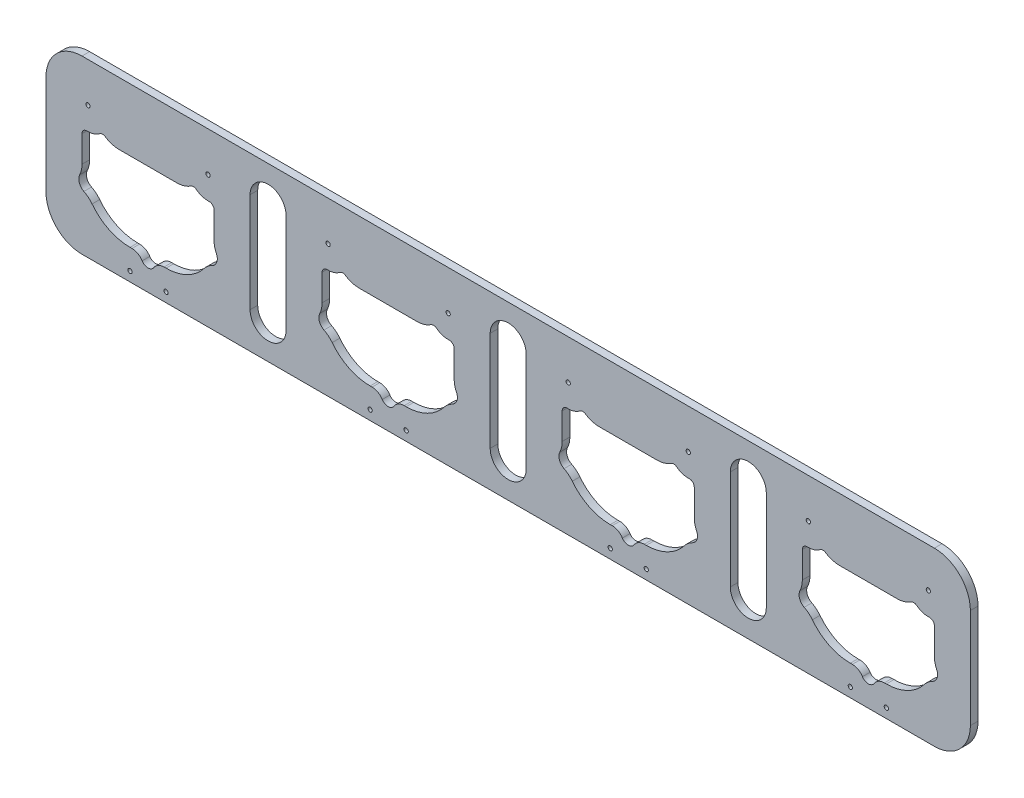
SolidWorks part; units mm, degrees
ref_plane "Front Plane" through (0, 0, 0) normal (0, 0, 1) x (1, 0, 0)
ref_plane "Top Plane" through (0, 0, 0) normal (0, 1, 0) x (1, 0, 0)
ref_plane "Right Plane" through (0, 0, 0) normal (1, 0, 0) x (0, 0, -1)
sketch "Sketch1" plane through (0, 0, 0) normal (0, 0, 1) x (1, 0, 0)
  line L1 (-5.296, 23.9144) -> (18.704, 23.9144)
  line L3 (13.382, -9.0856) -> (14.204, -9.0856)
  line L10 (34.204, 10.9144) -> (34.204, 21.927)
  line L11 (-0.796, -9.0856) -> (0.0259, -9.0856)
  line L12 (-20.796, 10.9144) -> (-20.796, 21.927)
  line L50 (94.704, 23.9144) -> (118.704, 23.9144)
  line L52 (113.382, -9.0856) -> (114.204, -9.0856)
  line L59 (134.204, 10.9144) -> (134.204, 21.927)
  line L60 (99.204, -9.0856) -> (100.0259, -9.0856)
  line L61 (79.204, 10.9144) -> (79.204, 21.927)
  line L74 (149.204, 34.9144) -> (149.204, -6.5856)
  line L75 (164.204, -6.5856) -> (164.204, 34.9144)
  line L77 (194.704, 23.9144) -> (218.704, 23.9144)
  line L79 (213.382, -9.0856) -> (214.204, -9.0856)
  line L86 (234.204, 10.9144) -> (234.204, 21.927)
  line L87 (199.204, -9.0856) -> (200.0259, -9.0856)
  line L88 (179.204, 10.9144) -> (179.204, 21.927)
  line L101 (249.204, 34.9144) -> (249.204, -6.5856)
  line L102 (264.204, -6.5856) -> (264.204, 34.9144)
  line L104 (294.704, 23.9144) -> (318.704, 23.9144)
  line L106 (313.382, -9.0856) -> (314.204, -9.0856)
  line L113 (334.204, 10.9144) -> (334.204, 21.927)
  line L114 (299.204, -9.0856) -> (300.0259, -9.0856)
  line L115 (279.204, 10.9144) -> (279.204, 21.927)
  line L153 (49.204, 34.9144) -> (49.204, -6.5856)
  line L154 (64.204, -6.5856) -> (64.204, 34.9144)
  line L159 (-20.796, 49.9144) -> (334.204, 49.9144)
  line L160 (-35.796, 34.9144) -> (-35.796, -6.5856)
  line L161 (-20.796, -21.5856) -> (334.204, -21.5856)
  line L162 (349.204, -6.5856) -> (349.204, 34.9144)
  line L163 (364.204, -6.5856) -> (364.204, 34.9144) [skipped]
  line L164 (349.204, 34.9144) -> (349.204, -6.5856) [skipped]
  arc A0 (24.4994, 25.6587) -> (18.704, 23.9144) centre (18.704, 34.4144) cw
  arc A1 (34.2039, 10.8952) -> (34.204, 10.9144) centre (14.204, 10.9144) ccw
  arc A6 (-16.6004, -1.3421) -> (-0.796, -9.0856) centre (-0.796, 10.9144) ccw
  arc A7 (34.2039, 10.8952) -> (35.1806, 6.5752) centre (44.2039, 10.8855) ccw
  arc A24 (-11.0915, 25.6587) -> (-13.4155, 25.5756) centre (-12.1954, 23.9909) ccw
  arc A25 (-20.796, 21.927) -> (-18.696, 23.9245) centre (-18.796, 21.927) cw
  arc A26 (26.8234, 25.5756) -> (32.104, 23.9245) centre (31.704, 31.9144) ccw
  arc A28 (26.8234, 25.5756) -> (24.4994, 25.6587) centre (25.6033, 23.9909) ccw
  arc A29 (14.204, -9.0856) -> (30.0083, -1.3421) centre (14.204, 10.9144) ccw
  arc A30 (-20.796, 10.9144) -> (-20.796, 10.8952) centre (-0.796, 10.9144) ccw
  arc A31 (30.0083, -1.3421) -> (33.4302, 1.4699) centre (37.9105, -7.4703) cw
  arc A33 (-18.696, 23.9245) -> (-13.4155, 25.5756) centre (-18.296, 31.9144) ccw
  arc A34 (-16.6004, -1.3421) -> (-20.0223, 1.4699) centre (-24.5026, -7.4703) ccw
  arc A36 (-20.796, 10.8952) -> (-21.7727, 6.5752) centre (-30.796, 10.8855) cw
  arc A37 (4.2584, -11.4236) -> (0.0259, -9.0856) centre (0.0259, -14.0856) ccw
  arc A38 (-11.0915, 25.6587) -> (-5.296, 23.9144) centre (-5.296, 34.4144) ccw
  arc A39 (-21.7727, 6.5752) -> (-20.0223, 1.4699) centre (-18.296, 4.9144) ccw
  arc A40 (33.4302, 1.4699) -> (35.1806, 6.5752) centre (31.704, 4.9144) ccw
  arc A41 (4.2584, -11.4236) -> (9.1495, -11.4236) centre (6.704, -9.8856) ccw
  arc A43 (34.204, 21.927) -> (32.104, 23.9245) centre (32.204, 21.927) ccw
  arc A44 (9.1495, -11.4236) -> (13.382, -9.0856) centre (13.382, -14.0856) cw
  arc A109 (124.4994, 25.6587) -> (118.704, 23.9144) centre (118.704, 34.4144) cw
  arc A110 (134.2039, 10.8952) -> (134.204, 10.9144) centre (114.204, 10.9144) ccw
  arc A115 (83.3996, -1.3421) -> (99.204, -9.0856) centre (99.204, 10.9144) ccw
  arc A116 (134.2039, 10.8952) -> (135.1806, 6.5752) centre (144.2039, 10.8855) ccw
  arc A133 (88.9085, 25.6587) -> (86.5845, 25.5756) centre (87.8046, 23.9909) ccw
  arc A134 (79.204, 21.927) -> (81.304, 23.9245) centre (81.204, 21.927) cw
  arc A135 (126.8234, 25.5756) -> (132.104, 23.9245) centre (131.704, 31.9144) ccw
  arc A137 (126.8234, 25.5756) -> (124.4994, 25.6587) centre (125.6033, 23.9909) ccw
  arc A138 (114.204, -9.0856) -> (130.0083, -1.3421) centre (114.204, 10.9144) ccw
  arc A139 (79.204, 10.9144) -> (79.204, 10.8952) centre (99.204, 10.9144) ccw
  arc A140 (130.0083, -1.3421) -> (133.4302, 1.4699) centre (137.9105, -7.4703) cw
  arc A142 (81.304, 23.9245) -> (86.5845, 25.5756) centre (81.704, 31.9144) ccw
  arc A143 (83.3996, -1.3421) -> (79.9777, 1.4699) centre (75.4974, -7.4703) ccw
  arc A144 (79.204, 10.8952) -> (78.2273, 6.5752) centre (69.204, 10.8855) cw
  arc A145 (104.2584, -11.4236) -> (100.0259, -9.0856) centre (100.0259, -14.0856) ccw
  arc A146 (88.9085, 25.6587) -> (94.704, 23.9144) centre (94.704, 34.4144) ccw
  arc A147 (78.2273, 6.5752) -> (79.9777, 1.4699) centre (81.704, 4.9144) ccw
  arc A148 (133.4302, 1.4699) -> (135.1806, 6.5752) centre (131.704, 4.9144) ccw
  arc A149 (104.2584, -11.4236) -> (109.1495, -11.4236) centre (106.704, -9.8856) ccw
  arc A150 (134.204, 21.927) -> (132.104, 23.9245) centre (132.204, 21.927) ccw
  arc A151 (109.1495, -11.4236) -> (113.382, -9.0856) centre (113.382, -14.0856) cw
  arc A152 (64.204, 34.9144) -> (49.204, 34.9144) centre (56.704, 34.9144) ccw
  arc A153 (49.204, -6.5856) -> (64.204, -6.5856) centre (56.704, -6.5856) ccw
  arc A158 (-20.796, 49.9144) -> (-35.796, 34.9144) centre (-20.796, 34.9144) ccw
  arc A159 (-35.796, -6.5856) -> (-20.796, -21.5856) centre (-20.796, -6.5856) ccw
  arc A160 (334.204, -21.5856) -> (349.204, -6.5856) centre (334.204, -6.5856) ccw
  arc A161 (334.204, 49.9144) -> (349.204, 34.9144) centre (334.204, 34.9144) cw
  circle A162 centre (-18.296, 33.4144) radius 0.889
  circle A163 centre (31.704, 33.4144) radius 0.889
  circle A164 centre (14.204, -17.6203) radius 0.889
  circle A165 centre (-0.796, -17.6203) radius 0.889
  arc A168 (164.204, 34.9144) -> (149.204, 34.9144) centre (156.704, 34.9144) ccw
  arc A169 (149.204, -6.5856) -> (164.204, -6.5856) centre (156.704, -6.5856) ccw
  circle A170 centre (81.704, 33.4144) radius 0.889
  circle A171 centre (131.704, 33.4144) radius 0.889
  circle A172 centre (114.204, -17.6203) radius 0.889
  circle A173 centre (99.204, -17.6203) radius 0.889
  arc A174 (224.4994, 25.6587) -> (218.704, 23.9144) centre (218.704, 34.4144) cw
  arc A175 (234.2039, 10.8952) -> (234.204, 10.9144) centre (214.204, 10.9144) ccw
  arc A180 (183.3996, -1.3421) -> (199.204, -9.0856) centre (199.204, 10.9144) ccw
  arc A181 (234.2039, 10.8952) -> (235.1806, 6.5752) centre (244.2039, 10.8855) ccw
  arc A198 (188.9085, 25.6587) -> (186.5845, 25.5756) centre (187.8046, 23.9909) ccw
  arc A199 (179.204, 21.927) -> (181.304, 23.9245) centre (181.204, 21.927) cw
  arc A200 (226.8234, 25.5756) -> (232.104, 23.9245) centre (231.704, 31.9144) ccw
  arc A202 (226.8234, 25.5756) -> (224.4994, 25.6587) centre (225.6033, 23.9909) ccw
  arc A203 (214.204, -9.0856) -> (230.0083, -1.3421) centre (214.204, 10.9144) ccw
  arc A204 (179.204, 10.9144) -> (179.204, 10.8952) centre (199.204, 10.9144) ccw
  arc A205 (230.0083, -1.3421) -> (233.4302, 1.4699) centre (237.9105, -7.4703) cw
  arc A207 (181.304, 23.9245) -> (186.5845, 25.5756) centre (181.704, 31.9144) ccw
  arc A208 (183.3996, -1.3421) -> (179.9777, 1.4699) centre (175.4974, -7.4703) ccw
  arc A209 (179.204, 10.8952) -> (178.2273, 6.5752) centre (169.204, 10.8855) cw
  arc A210 (204.2584, -11.4236) -> (200.0259, -9.0856) centre (200.0259, -14.0856) ccw
  arc A211 (188.9085, 25.6587) -> (194.704, 23.9144) centre (194.704, 34.4144) ccw
  arc A212 (178.2273, 6.5752) -> (179.9777, 1.4699) centre (181.704, 4.9144) ccw
  arc A213 (233.4302, 1.4699) -> (235.1806, 6.5752) centre (231.704, 4.9144) ccw
  arc A214 (204.2584, -11.4236) -> (209.1495, -11.4236) centre (206.704, -9.8856) ccw
  arc A215 (234.204, 21.927) -> (232.104, 23.9245) centre (232.204, 21.927) ccw
  arc A216 (209.1495, -11.4236) -> (213.382, -9.0856) centre (213.382, -14.0856) cw
  arc A223 (264.204, 34.9144) -> (249.204, 34.9144) centre (256.704, 34.9144) ccw
  arc A224 (249.204, -6.5856) -> (264.204, -6.5856) centre (256.704, -6.5856) ccw
  circle A225 centre (181.704, 33.4144) radius 0.889
  circle A226 centre (231.704, 33.4144) radius 0.889
  circle A227 centre (214.204, -17.6203) radius 0.889
  circle A228 centre (199.204, -17.6203) radius 0.889
  arc A229 (324.4994, 25.6587) -> (318.704, 23.9144) centre (318.704, 34.4144) cw
  arc A230 (334.2039, 10.8952) -> (334.204, 10.9144) centre (314.204, 10.9144) ccw
  arc A235 (283.3996, -1.3421) -> (299.204, -9.0856) centre (299.204, 10.9144) ccw
  arc A236 (334.2039, 10.8952) -> (335.1806, 6.5752) centre (344.2039, 10.8855) ccw
  arc A253 (288.9085, 25.6587) -> (286.5845, 25.5756) centre (287.8046, 23.9909) ccw
  arc A254 (279.204, 21.927) -> (281.304, 23.9245) centre (281.204, 21.927) cw
  arc A255 (326.8234, 25.5756) -> (332.104, 23.9245) centre (331.704, 31.9144) ccw
  arc A257 (326.8234, 25.5756) -> (324.4994, 25.6587) centre (325.6033, 23.9909) ccw
  arc A258 (314.204, -9.0856) -> (330.0083, -1.3421) centre (314.204, 10.9144) ccw
  arc A259 (279.204, 10.9144) -> (279.204, 10.8952) centre (299.204, 10.9144) ccw
  arc A260 (330.0083, -1.3421) -> (333.4302, 1.4699) centre (337.9105, -7.4703) cw
  arc A262 (281.304, 23.9245) -> (286.5845, 25.5756) centre (281.704, 31.9144) ccw
  arc A263 (283.3996, -1.3421) -> (279.9777, 1.4699) centre (275.4974, -7.4703) ccw
  arc A264 (279.204, 10.8952) -> (278.2273, 6.5752) centre (269.204, 10.8855) cw
  arc A265 (304.2584, -11.4236) -> (300.0259, -9.0856) centre (300.0259, -14.0856) ccw
  arc A266 (288.9085, 25.6587) -> (294.704, 23.9144) centre (294.704, 34.4144) ccw
  arc A267 (278.2273, 6.5752) -> (279.9777, 1.4699) centre (281.704, 4.9144) ccw
  arc A268 (333.4302, 1.4699) -> (335.1806, 6.5752) centre (331.704, 4.9144) ccw
  arc A269 (304.2584, -11.4236) -> (309.1495, -11.4236) centre (306.704, -9.8856) ccw
  arc A270 (334.204, 21.927) -> (332.104, 23.9245) centre (332.204, 21.927) ccw
  arc A271 (309.1495, -11.4236) -> (313.382, -9.0856) centre (313.382, -14.0856) cw
  circle A280 centre (281.704, 33.4144) radius 0.889
  circle A281 centre (331.704, 33.4144) radius 0.889
  circle A282 centre (314.204, -17.6203) radius 0.889
  circle A283 centre (299.204, -17.6203) radius 0.889
  arc A284 (364.204, 34.9144) -> (349.204, 34.9144) centre (356.704, 34.9144) ccw [skipped]
  arc A285 (349.204, -6.5856) -> (364.204, -6.5856) centre (356.704, -6.5856) ccw [skipped]
  point P6 (33.4759, 5.4562)
  point P22 (-18.296, 4.9144)
  point P24 (31.704, 4.9144)
  point P109 (9.593, -9.8856)
  point P126 (-16.5241, 5.4562)
  dimension "D7" = 5
  dimension "D8" = 5
  dimension "D32" = 4
  dimension "D34" = 15
  dimension "D35" = 15
  dimension "D12" = 2
extrude "Boss-Extrude1" add sketch "Sketch1" along normal blind 3.175
